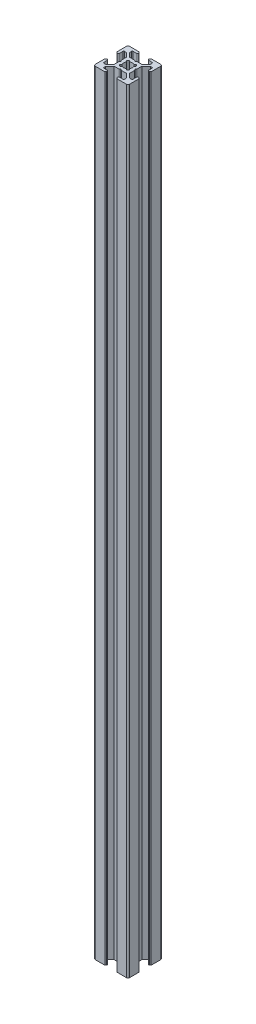
SolidWorks part; units mm, degrees
ref_plane "Front Plane" through (0, 0, 0) normal (0, 0, 1) x (1, 0, 0)
ref_plane "Top Plane" through (0, 0, 0) normal (0, 1, 0) x (1, 0, 0)
ref_plane "Right Plane" through (0, 0, 0) normal (1, 0, 0) x (0, 0, -1)
sketch "Sketch3" plane through (0, 0, 0) normal (0, 1, 0) x (1, 0, 0)
  line L0 (7, 20) -> (7, 18.5)
  line L1 (0, 0) -> (20, 0)
  line L2 (0, 0) -> (0, 20)
  line L3 (0, 20) -> (20, 20)
  line L4 (20, 0) -> (20, 20)
  line L5 (7, 18.5) -> (4, 18.5)
  line L6 (4, 18.5) -> (4, 17)
  line L7 (4, 17) -> (6.5, 14.5)
  line L8 (6.5, 14.5) -> (13.5, 14.5)
  line L9 (13.5, 14.5) -> (16, 17)
  line L10 (16, 17) -> (16, 18.5)
  line L11 (16, 18.5) -> (13, 18.5)
  line L12 (13, 18.5) -> (13, 20)
  line L13 (13, 20) -> (7, 20)
  line L14 (9.5, 14.5) -> (10, 14)
  line L15 (10, 14) -> (10.5, 14.5)
  line L16 (10.5, 14.5) -> (9.5, 14.5)
  line L17 (13, 19.5) -> (13, 20)
  line L18 (13.5, 20) -> (13, 20)
  line L19 (7, 19.5) -> (7, 20)
  line L20 (6.5, 20) -> (7, 20)
  line L21 (0, 13) -> (1.5, 13)
  line L22 (1.5, 13) -> (1.5, 16)
  line L23 (1.5, 16) -> (3, 16)
  line L24 (3, 16) -> (5.5, 13.5)
  line L25 (5.5, 13.5) -> (5.5, 6.5)
  line L26 (5.5, 6.5) -> (3, 4)
  line L27 (3, 4) -> (1.5, 4)
  line L28 (1.5, 4) -> (1.5, 7)
  line L29 (1.5, 7) -> (0, 7)
  line L30 (0, 7) -> (0, 13)
  line L31 (5.5, 10.5) -> (5.5, 9.5)
  line L32 (5.5, 9.5) -> (6, 10)
  line L33 (6, 10) -> (5.5, 10.5)
  line L34 (0.5, 13) -> (0, 13)
  line L35 (0, 13.5) -> (0, 13)
  line L36 (0, 6.5) -> (0, 7)
  line L37 (0.5, 7) -> (0, 7)
  line L38 (10, 20) -> (10, 0) construction
  line L39 (20, 10) -> (0, 10) construction
  line L40 (10, 6) -> (10.5, 5.5)
  line L41 (9.5, 5.5) -> (10, 6)
  line L42 (10.5, 5.5) -> (9.5, 5.5)
  line L43 (13.5, 0) -> (13, 0)
  line L44 (13, 0.5) -> (13, 0)
  line L45 (6.5, 0) -> (7, 0)
  line L46 (7, 0.5) -> (7, 0)
  line L47 (13, 1.5) -> (13, 0)
  line L48 (16, 1.5) -> (13, 1.5)
  line L49 (16, 3) -> (16, 1.5)
  line L50 (13.5, 5.5) -> (16, 3)
  line L51 (6.5, 5.5) -> (13.5, 5.5)
  line L52 (4, 3) -> (6.5, 5.5)
  line L53 (4, 1.5) -> (4, 3)
  line L54 (7, 1.5) -> (4, 1.5)
  line L55 (7, 0) -> (7, 1.5)
  line L56 (13, 0) -> (7, 0)
  line L57 (14.5, 9.5) -> (14, 10)
  line L58 (14.5, 10.5) -> (14.5, 9.5)
  line L59 (14, 10) -> (14.5, 10.5)
  line L60 (19.5, 7) -> (20, 7)
  line L61 (20, 6.5) -> (20, 7)
  line L62 (20, 13.5) -> (20, 13)
  line L63 (19.5, 13) -> (20, 13)
  line L64 (18.5, 7) -> (20, 7)
  line L65 (18.5, 4) -> (18.5, 7)
  line L66 (17, 4) -> (18.5, 4)
  line L67 (14.5, 6.5) -> (17, 4)
  line L68 (14.5, 13.5) -> (14.5, 6.5)
  line L69 (17, 16) -> (14.5, 13.5)
  line L70 (18.5, 16) -> (17, 16)
  line L71 (18.5, 13) -> (18.5, 16)
  line L72 (20, 13) -> (18.5, 13)
  line L73 (20, 7) -> (20, 13)
  arc A0 (13.5, 20) -> (13, 19.5) centre (13, 20) cw
  arc A1 (6.5, 20) -> (7, 19.5) centre (7, 20) ccw
  arc A2 (0.5, 13) -> (0, 13.5) centre (0, 13) ccw
  arc A3 (0.5, 7) -> (0, 6.5) centre (0, 7) cw
  arc A4 (13.5, 0) -> (13, 0.5) centre (13, 0) ccw
  arc A5 (6.5, 0) -> (7, 0.5) centre (7, 0) cw
  arc A6 (19.5, 7) -> (20, 6.5) centre (20, 7) ccw
  arc A7 (19.5, 13) -> (20, 13.5) centre (20, 13) cw
  point P7 (10, 14.5)
  point P16 (10, 20)
  point P26 (5.5, 10)
  point P35 (0, 10)
  dimension "D16" = 0.5
  dimension "D17" = 0.5
  dimension "D28" = 0.5
  dimension "D29" = 0.5
  dimension "D1" = 20
  dimension "D2" = 20
  dimension "D3" = 7
  dimension "D4" = 7
  dimension "D5" = 1.5
  dimension "D6" = 1.5
  dimension "D7" = 3
  dimension "D8" = 3
  dimension "D9" = 1.5
  dimension "D10" = 1.5
  dimension "D11" = 7
  dimension "D12" = 5.5
  dimension "D13" = 0.5
  dimension "D14" = 0.5
  dimension "D15" = 0.5
  dimension "D18" = 7
  dimension "D19" = 7
  dimension "D20" = 1.5
  dimension "D21" = 1.5
  dimension "D22" = 3
  dimension "D23" = 7
  dimension "D24" = 5.5
  dimension "D25" = 0.5
  dimension "D26" = 0.5
  dimension "D27" = 0.5
extrude "Boss-Extrude1" add sketch "Sketch3" along normal blind 450 contours L72 A7 L4 L3 A0 L12 L11 L10 L9 L8 L15 L14 L7 L6 L5 L0 A1 L2 A2 L21 L22 L23 L24 L25 L33 L32 L26 L27 L28 L29 A3 L1 A5 L55 L54 L53 L52 L51 L41 L40 L50 L49 L48 L47 A4
fillet "Fillet1" radius 1 4 edges at (0, 225, 0) (20, 225, 0) (20, 225, -20) (0, 225, -20)
sketch "Sketch4" plane through (0, 450, 0) normal (0, 1, 0) x (1, 0, 0)
  line L0 (13.5, 14.5) -> (5.5, 6.5) construction
  line L1 (14.5, 13.5) -> (6.5, 5.5) construction
  line L2 (10.5, 14.5) -> (14.5, 10.5) construction
  line L3 (12, 13) -> (13, 12)
  line L4 (13, 12) -> (8, 7)
  line L5 (8, 7) -> (7, 8)
  line L6 (7, 8) -> (12, 13)
  line L7 (13.5, 14.5) -> (16, 17) construction
  line L8 (17, 16) -> (14.5, 13.5) construction
  line L9 (5.5, 9.5) -> (9.5, 5.5) construction
  line L10 (5.5, 10.5) -> (9.5, 14.5) construction
  line L11 (14.5, 9.5) -> (10.5, 5.5) construction
  line L12 (6.5, 14.5) -> (14.5, 6.5) construction
  line L13 (5.5, 13.5) -> (13.5, 5.5) construction
  line L14 (7, 12) -> (8, 13)
  line L15 (8, 13) -> (13, 8)
  line L16 (13, 8) -> (12, 7)
  line L17 (12, 7) -> (7, 12)
  line L18 (4, 17) -> (6.5, 14.5) construction
  line L19 (3, 16) -> (5.5, 13.5) construction
  line L20 (20, 10) -> (0, 10) construction
  circle A0 centre (10, 10) radius 2.5
  dimension "D1" = 5
extrude "Cut-Extrude1" cut sketch "Sketch4" against normal through all contours L6 A0 L15 | L4 A0 L6 L15 | L15 A0 L17 L6 | L17 L4 L15 L6 | L17 A0 L6 | L6 A0 L4 L17 | L4 A0 L17 | L17 A0 L15 L4 | L15 A0 L4 | A0 L6 L5 L4 | A0 L17 L16 L15 | A0 L4 L3 L6 | A0 L15 L14 L17
fillet "Fillet2" radius 0.5 24 edges at (1.5, 225, -16) (1.5, 225, -13) (5.5, 225, -10.5) (5.5, 225, -9.5) (1.5, 225, -7) (1.5, 225, -4) (4, 225, -1.5) (7, 225, -1.5) (9.5, 225, -5.5) (10.5, 225, -5.5) (13, 225, -1.5) (16, 225, -1.5) (18.5, 225, -4) (18.5, 225, -7) (18.5, 225, -13) (18.5, 225, -16) (14.5, 225, -9.5) (14.5, 225, -10.5) (10.5, 225, -14.5) (9.5, 225, -14.5) (16, 225, -18.5) (13, 225, -18.5) (7, 225, -18.5) (4, 225, -18.5)
fillet "Fillet3" radius 0.25 8 edges at (13, 225, -8) (12, 225, -7) (13, 225, -12) (12, 225, -13) (8, 225, -13) (7, 225, -12) (7, 225, -8) (8, 225, -7)
